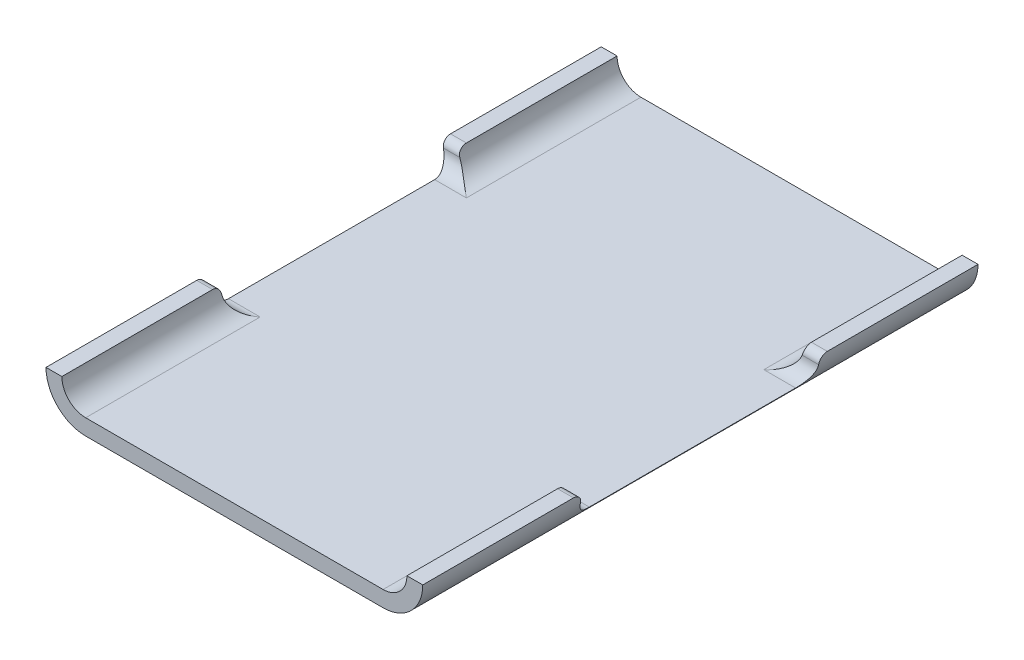
SolidWorks part; units mm, degrees
ref_plane "Front" through (0, 0, 0) normal (0, 0, 1) x (1, 0, 0)
ref_plane "Top" through (0, 0, 0) normal (0, 1, 0) x (1, 0, 0)
ref_plane "Right" through (0, 0, 0) normal (1, 0, 0) x (0, 0, -1)
sketch "Sketch2" plane through (0, 0, 0) normal (0, 1, 0) x (1, 0, 0)
  line L0 (0, 0) -> (47.5, 0)
  line L1 (47.5, 0) -> (47.5, -70)
  line L2 (47.5, -70) -> (0, -70)
  line L3 (0, -70) -> (0, 0)
  dimension "D1" = 47.5
  dimension "D2" = 70
extrude "Boss-Extrude1" add sketch "Sketch2" along normal blind 5
sketch "Sketch4" plane through (0, 0, 0) normal (-1, 0, 0) x (0, 0, 1)
  line L6 (19, 5) -> (51, 5)
  line L10 (22, 2) -> (48, 2)
  arc A0 (20, 4) -> (19, 5) centre (19, 4) ccw
  arc A1 (51, 5) -> (50, 4) centre (51, 4) ccw
  arc A2 (20, 4) -> (22, 2) centre (22, 4) ccw
  arc A3 (48, 2) -> (50, 4) centre (48, 4) ccw
extrude "Cut-Extrude2" cut sketch "Sketch4" against normal through all
sketch "Sketch3" plane through (0, 0, 70) normal (0, 0, 1) x (1, 0, 0)
  line L1 (0, 5) -> (47.5, 5) construction
  line L2 (0, 0) -> (47.5, 0) construction
  line L4 (5, 2) -> (42.5, 2)
  line L5 (2, 5) -> (45.5, 5)
  line L6 (42.5, 0) -> (47.5, 0)
  line L7 (0, 5) -> (0, 0)
  line L8 (0, 0) -> (5, 0)
  line L9 (47.5, 0) -> (47.5, 5)
  arc A0 (2, 5) -> (5, 2) centre (5, 5) ccw
  arc A1 (0, 5) -> (5, 0) centre (5, 5) ccw
  arc A2 (42.5, 2) -> (45.5, 5) centre (42.5, 5) ccw
  arc A3 (42.5, 0) -> (47.5, 5) centre (42.5, 5) ccw
extrude "Cut-Extrude1" cut sketch "Sketch3" against normal through all
sketch "Sketch6" plane through (0, 0, 0) normal (0, -1, 0) x (1, 0, 0)
  line L6 (28.75, 35) -> (28.75, 42.5)
  line L7 (28.75, 35) -> (28.75, 27.5)
  line L10 (18.75, 42.5) -> (18.75, 27.5)
  arc A0 (28.75, 42.5) -> (18.75, 42.5) centre (23.75, 42.5) ccw
  arc A1 (18.75, 27.5) -> (28.75, 27.5) centre (23.75, 27.5) ccw
extrude "Cut-Extrude3" cut sketch "Sketch6" against normal blind 0.5
sketch "Sketch5" plane through (0, 0, 0) normal (0, -1, 0) x (1, 0, 0)
  line L25 (21.25, 40.482) -> (21.25, 35.982)
  line L26 (26.25, 40.482) -> (26.25, 35.982)
  line L27 (19.75, 33.982) -> (21.25, 33.982)
  line L28 (21.25, 42.482) -> (19.75, 42.482)
  line L29 (19.75, 42.482) -> (19.75, 40.482)
  line L30 (19.75, 40.482) -> (21.25, 40.482)
  line L31 (21.25, 33.982) -> (21.25, 29.482)
  line L32 (21.25, 27.482) -> (19.75, 27.482)
  line L33 (19.75, 27.482) -> (19.75, 29.482)
  line L34 (19.75, 29.482) -> (21.25, 29.482)
  line L35 (21.25, 35.982) -> (19.75, 35.982)
  line L36 (19.75, 35.982) -> (19.75, 33.982)
  line L37 (26.25, 42.482) -> (27.75, 42.482)
  line L38 (27.75, 35.982) -> (27.75, 33.982)
  line L39 (26.25, 35.982) -> (27.75, 35.982)
  line L40 (27.75, 29.482) -> (26.25, 29.482)
  line L41 (27.75, 27.482) -> (27.75, 29.482)
  line L42 (26.25, 27.482) -> (27.75, 27.482)
  line L43 (27.75, 40.482) -> (26.25, 40.482)
  line L44 (27.75, 42.482) -> (27.75, 40.482)
  line L45 (27.75, 33.982) -> (26.25, 33.982)
  line L46 (26.25, 33.982) -> (26.25, 29.482)
  arc A2 (26.25, 42.482) -> (21.25, 42.482) centre (23.75, 42.482) ccw
  arc A3 (21.25, 27.482) -> (26.25, 27.482) centre (23.75, 27.482) ccw
  point P6 (0, 0)
  point P34 (0, 0)
  point P35 (0, 0)
  dimension "D1" = 5
  dimension "D2" = 2
  dimension "D3" = 4.5
extrude "Boss-Extrude2" add sketch "Sketch5" along normal blind 14 separate body
chamfer "Chamfer1" distance 1 angle 45 6 edges at (27.75, -14, 28.482) (27.75, -14, 34.982) (27.75, -14, 41.482) (19.75, -14, 41.482) (19.75, -14, 34.982) (19.75, -14, 28.482)
